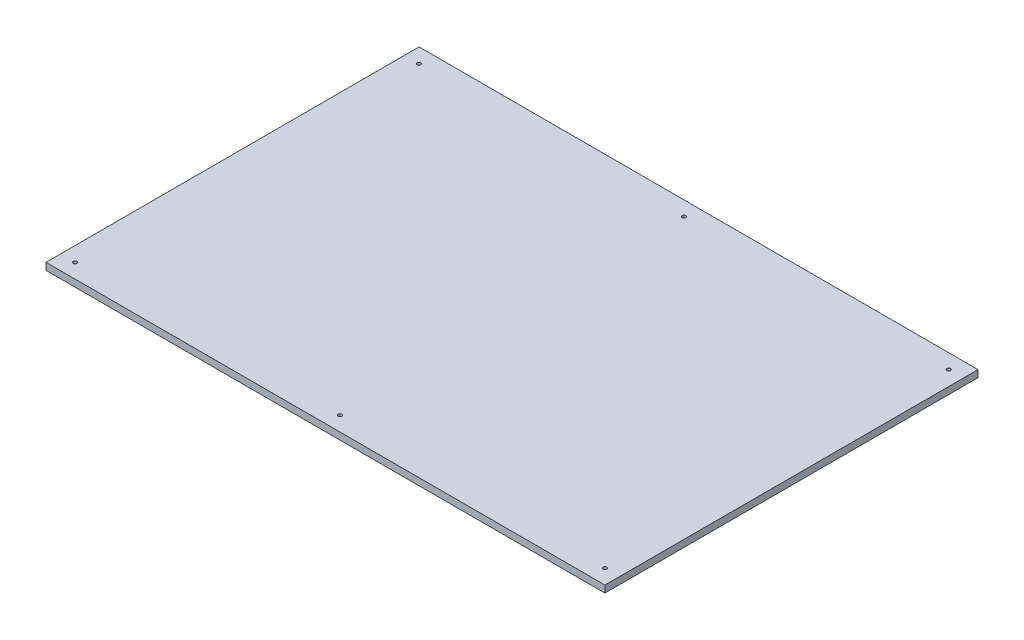
SolidWorks part; units mm, degrees
ref_plane "Front" through (0, 0, 0) normal (0, 0, 1) x (1, 0, 0)
ref_plane "Top" through (0, 0, 0) normal (0, 1, 0) x (1, 0, 0)
ref_plane "Right" through (0, 0, 0) normal (1, 0, 0) x (0, 0, -1)
sketch "Sketch1" plane through (0, 0, 0) normal (0, 1, 0) x (1, 0, 0)
  line L0 (962, 0) -> (-962, 0) construction
  line L1 (-1015, 802.5) -> (1015, 802.5)
  line L2 (-1015, 802.5) -> (-1015, -552.5)
  line L3 (-1015, -552.5) -> (1015, -552.5)
  line L4 (1015, 802.5) -> (1015, -552.5)
  line L5 (0, -552.5) -> (0, 802.5) construction
  line L6 (-1015, 0) -> (1015, 0) construction
  line L7 (-962, 749.5) -> (962, 749.5) construction
  line L8 (962, 749.5) -> (962, -499.5) construction
  line L9 (-1000, 787.5) -> (1000, 787.5) construction
  line L10 (1000, 787.5) -> (1000, -537.5) construction
  line L11 (-1000, -537.5) -> (1000, -537.5) construction
  line L12 (-1000, 787.5) -> (-1000, -537.5) construction
  line L13 (-962, -499.5) -> (962, -499.5) construction
  line L14 (-962, 749.5) -> (-962, -499.5) construction
  line L17 (962, 749.5) -> (-962, 749.5) construction
  point P5 (962, 749.5)
  point P6 (962, -499.5)
  point P9 (-962, -499.5)
  point P29 (-962, 749.5)
  point P136 (0, 0)
  dimension "D1" = 15
  dimension "D2" = 1015
  dimension "D3" = 1015
  dimension "D4" = 802.5
  dimension "D5" = 552.5
  dimension "D6" = 38
extrude "Boss-Extrude1" add sketch "Sketch1" along normal blind 25.4
hole_wizard "CBORE for M12 SHCS1" positions "Sketch2" profile "Sketch4" counterbore size "M12" standard "ANSI Metric" end condition through all
sketch "Sketch2" plane through (0, 0, 0) normal (0, -1, 0) x (-1, 0, 0)
  line L0 (-936.6, -474.1) -> (-987.4, -524.9) construction
  line L1 (-987.4, 774.9) -> (-936.6, 724.1) construction
  line L2 (936.6, 724.1) -> (987.4, 774.9) construction
  point P0 (-962, -499.5)
  point P4 (-962, 749.5)
  point P8 (0, 749.5)
  point P11 (962, 749.5)
  point P15 (962, -499.5)
  point P18 (0, -499.5)
sketch "Sketch4" plane through (962, 0, 499.5) normal (1, 0, 0) x (0, 0, -1)
  line L0 (0, 0) -> (0, 25.4)
  line L1 (0, 25.4) -> (6.75, 25.4)
  line L3 (6.75, 25.4) -> (6.75, 12)
  line L4 (6.75, 12) -> (10, 12)
  line L5 (10, 12) -> (10, 0)
  line L7 (10, 0) -> (0, 0)
  line L11 (0, -6.35) -> (0, 107.95) construction
  dimension "Thru Hole Dia." = 13.5
  dimension "Thru Hole Depth" = 25.4
  dimension "C'Bore Dia." = 20
  dimension "C'Bore Depth" = 12
